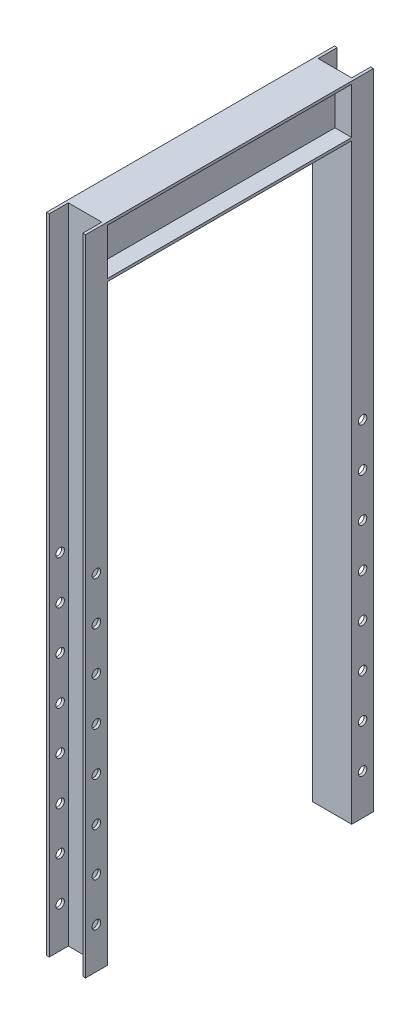
SolidWorks part; units mm, degrees
ref_plane "Front Plane" through (0, 0, 0) normal (0, 0, 1) x (1, 0, 0)
ref_plane "Top Plane" through (0, 0, 0) normal (0, 1, 0) x (1, 0, 0)
ref_plane "Right Plane" through (0, 0, 0) normal (1, 0, 0) x (0, 0, -1)
sketch "Sketch1" plane through (0, 0, 0) normal (0, 0, 1) x (1, 0, 0)
  line L0 (45.5295, 120.65) -> (45.5295, 114.3)
  line L1 (45.5295, 114.3) -> (6.35, 114.3)
  line L2 (6.35, 114.3) -> (6.35, 6.35)
  line L3 (6.35, 6.35) -> (45.5295, 6.35)
  line L4 (45.5295, 6.35) -> (45.5295, 0)
  line L6 (45.5295, 120.65) -> (0, 120.65)
  line L7 (0, 120.65) -> (0, 0)
  line L8 (0, 0) -> (45.5295, 0)
  dimension "D1" = 6.35
  dimension "D2" = 120.65
  dimension "D3" = 45.5295
  dimension "D4" = 6.35
extrude "Boss-Extrude1" add sketch "Sketch1" along normal mid plane 571.5
mirror "Mirror1" about plane through (0, 120.65, 285.75) normal (1, 0, 0) of "Boss-Extrude1"
sketch "Sketch3" plane through (0, 120.65, 0) normal (0, 1, 0) x (1, 0, 0)
  line L0 (-45.5295, -285.75) -> (45.5295, -285.75)
  line L1 (45.5295, -285.75) -> (45.5295, -336.55)
  line L2 (45.5295, -336.55) -> (39.1795, -336.55)
  line L3 (39.1795, -336.55) -> (39.1795, -292.1)
  line L4 (39.1795, -292.1) -> (-39.1795, -292.1)
  line L5 (-39.1795, -292.1) -> (-39.1795, -336.55)
  line L6 (-39.1795, -336.55) -> (-45.5295, -336.55)
  line L7 (-45.5295, -336.55) -> (-45.5295, -285.75)
  dimension "D1" = 6.35
  dimension "D2" = 6.35
  dimension "D3" = 50.8
extrude "Boss-Extrude2" add sketch "Sketch3" against normal blind 1504.95
sketch "Sketch4" plane through (45.5295, 0, 0) normal (1, 0, 0) x (0, 0, -1)
  line L0 (-311.15, 120.65) -> (-311.15, -577.85) construction
  line L1 (-336.55, 120.65) -> (285.75, 120.65) construction
  line L2 (-311.15, -577.85) -> (-285.75, -577.85) construction
  line L3 (-285.75, -1384.3) -> (-285.75, 0) construction
  line L4 (-311.15, -577.85) -> (-336.55, -577.85) construction
  line L5 (-336.55, -1384.3) -> (-336.55, 120.65) construction
  circle A0 centre (-311.15, -577.85) radius 10.033
  dimension "D2" = 20.066
  dimension "D1" = 698.5
extrude "Cut-Extrude1" cut sketch "Sketch4" against normal through all
pattern_linear "LPattern1" count 8 spacing 101.6 along (0, -1, 0) of "Cut-Extrude1"
mirror "Mirror2" about plane through (0, 0, 0) normal (0, 0, 1) of "LPattern1", "Cut-Extrude1", "Boss-Extrude2"
equation "\"D4@Sketch1\" = \"D1@Sketch1\""
equation "\"D2@Sketch3\" = \"D1@Sketch3\""
